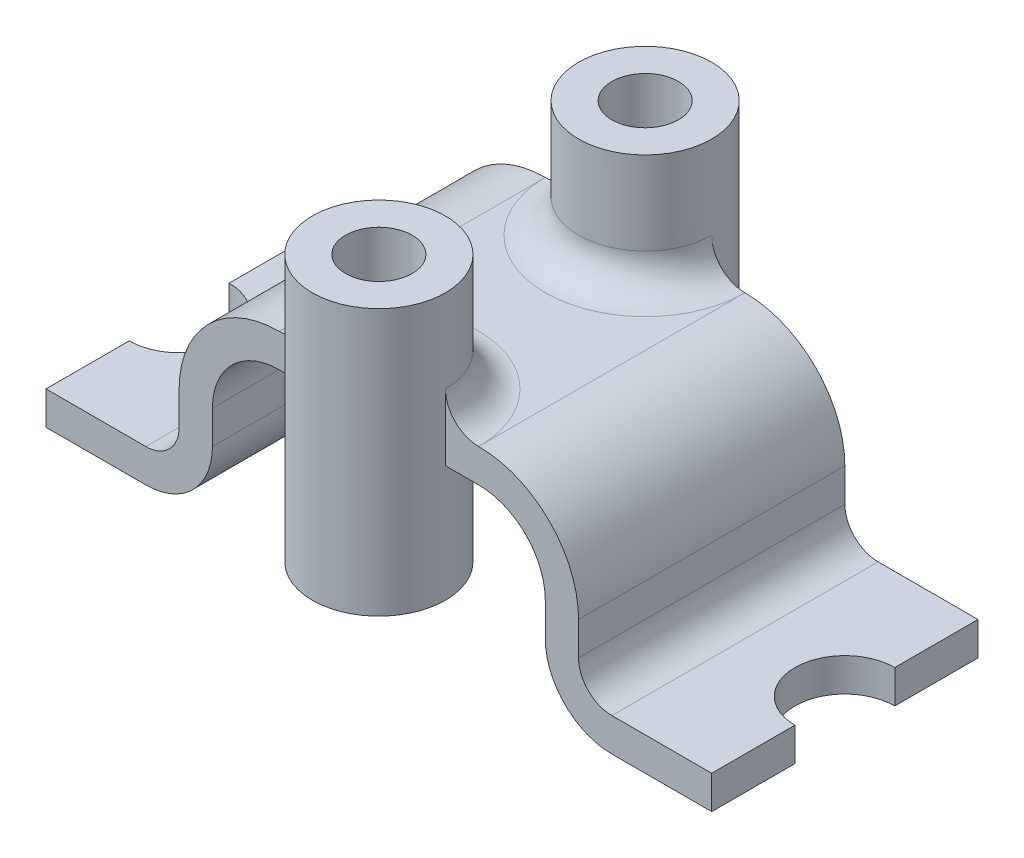
SolidWorks part; units mm, degrees
ref_plane "Front Plane" through (0, 0, 0) normal (0, 0, 1) x (1, 0, 0)
ref_plane "Top Plane" through (0, 0, 0) normal (0, 1, 0) x (1, 0, 0)
ref_plane "Right Plane" through (0, 0, 0) normal (1, 0, 0) x (0, 0, -1)
sketch "Sketch1" plane through (0, 0, 0) normal (0, 1, 0) x (1, 0, 0)
  line L1 (-30, 20) -> (30, 20)
  line L2 (-30, 20) -> (-30, -20)
  line L3 (-30, -20) -> (30, -20)
  line L4 (30, 20) -> (30, -20)
  line L5 (-30, 20) -> (30, -20) construction
  line L6 (-30, -20) -> (30, 20) construction
  point P0 (0, 0)
  dimension "D1" = 60
  dimension "D2" = 40
extrude "Boss-Extrude3" add sketch "Sketch1" along normal mid plane 5
sketch "Sketch3" plane through (0, 0, 0) normal (0, 1, 0) x (1, 0, 0)
  line L0 (-30, -20) -> (30, -20) construction
  line L1 (0, 0) -> (32.199, 0) construction
  circle A0 centre (0, -20) radius 5
  circle A1 centre (0, -20) radius 10
  circle A2 centre (0, 20) radius 5
  circle A3 centre (0, 20) radius 10
  dimension "D1" = 10
  dimension "D2" = 20
extrude "Boss-Extrude4" add sketch "Sketch3" along normal mid plane 40
fillet "Fillet7" radius 5 2 edges at (0, 2.5, -10) (0, 2.5, 10)
sketch "Sketch4" plane through (0, -2.5, 0) normal (0, -1, 0) x (1, 0, 0)
  line L0 (10, 20) -> (30, 20) construction
  line L1 (30, -20) -> (25, -20)
  line L2 (30, -20) -> (30, 20)
  line L3 (30, 20) -> (25, 20)
  line L4 (25, -20) -> (25, 20)
  line L6 (-30, -20) -> (-25, -20)
  line L7 (-30, -20) -> (-30, 20)
  line L8 (-30, 20) -> (-25, 20)
  line L9 (-25, -20) -> (-25, 20)
  dimension "D1" = 5
  dimension "D2" = 5
extrude "Boss-Extrude6" add sketch "Sketch4" along normal blind 25
sketch "Sketch5" plane through (30, 0, 0) normal (1, 0, 0) x (0, 0, -1)
  line L0 (20, 2.5) -> (20, -27.5) construction
  line L1 (-20, -27.5) -> (20, -27.5)
  line L2 (-20, -27.5) -> (-20, -22.5)
  line L3 (-20, -22.5) -> (20, -22.5)
  line L4 (20, -27.5) -> (20, -22.5)
  dimension "D1" = 5
extrude "Boss-Extrude7" add sketch "Sketch5" along normal blind 20 contours L2 L1 L4 L3
mirror "Mirror1" about plane through (0, 0, 0) normal (1, 0, 0) of "Boss-Extrude7"
fillet "Fillet8" radius 5 2 edges at (-30, -22.5, 0) (30, -22.5, 0)
fillet "Fillet9" radius 10 4 edges at (25, -2.5, 0) (-25, -2.5, 0) (25, -27.5, 0) (-25, -27.5, 0)
fillet "Fillet10" radius 15 2 edges at (30, 2.5, 0) (-30, 2.5, 0)
sketch "Sketch6" plane through (0, -22.5, 0) normal (0, 1, 0) x (1, 0, 0)
  line L0 (50, -20) -> (50, 20) construction
  line L1 (0, 0) -> (0, -20) construction
  line L2 (-5, -20) -> (5, -20) construction
  circle A0 centre (50, 0) radius 7.5
  circle A1 centre (-50, 0) radius 7.5
  dimension "D1" = 15
extrude "Cut-Extrude1" cut sketch "Sketch6" against normal blind 20
